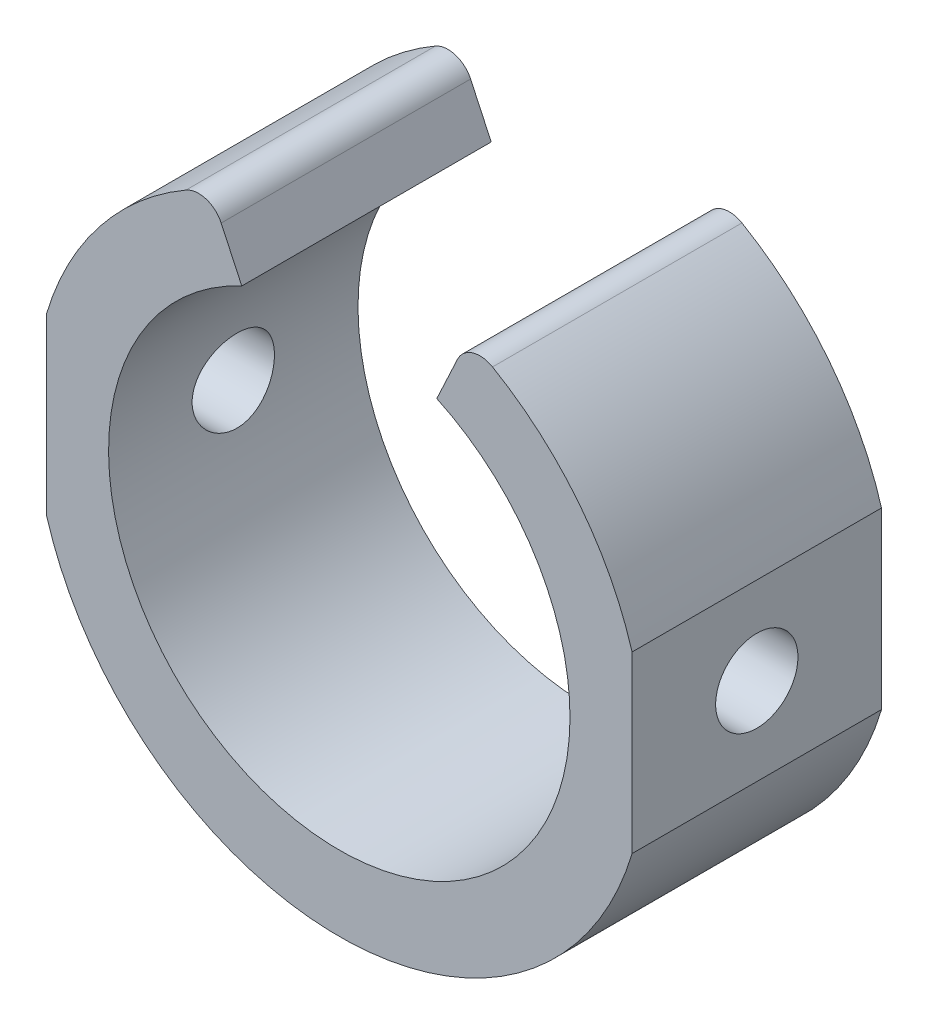
SolidWorks part; units mm, degrees
ref_plane "正面(Front)" through (0, 0, 0) normal (0, 0, 1) x (1, 0, 0)
ref_plane "平面(Top)" through (0, 0, 0) normal (0, 1, 0) x (1, 0, 0)
ref_plane "右側面(Right)" through (0, 0, 0) normal (1, 0, 0) x (0, 0, -1)
sketch "ｽｹｯﾁ1" plane through (0, 0, 0) normal (0, 0, 1) x (1, 0, 0)
  circle A0 centre (0, 0) radius 9.25
  circle A1 centre (0, 0) radius 12.25
  dimension "D1" = 18.5
  dimension "D2" = 3
extrude "ﾎﾞｽ - 押し出し1" add sketch "ｽｹｯﾁ1" along normal blind 10
sketch "ｽｹｯﾁ2" plane through (0, 0, 10) normal (0, 0, 1) x (1, 0, 0)
  line L0 (0, 0) -> (-7.0617, 15.144)
  line L1 (0, 0) -> (6.9061, 14.8103)
  line L2 (0, 0) -> (0, 17.4503) construction
  dimension "D1" = 25
extrude "ｶｯﾄ - 押し出し1" cut sketch "ｽｹｯﾁ2" against normal through all and the other way through all
sketch "ｽｹｯﾁ3" plane through (0, 0, 10) normal (0, 0, 1) x (1, 0, 0)
  line L0 (0, 0) -> (0, 8.3164) construction
  line L5 (-11.7394, -3.5) -> (-21.3781, -3.5)
  line L6 (-11.7394, -3.5) -> (-11.7394, 3.5)
  line L7 (-11.7394, 3.5) -> (-21.3781, 3.5)
  line L8 (-21.3781, -3.5) -> (-21.3781, 3.5)
  line L9 (11.7394, 3.5) -> (21.3781, 3.5)
  line L10 (21.3781, -3.5) -> (21.3781, 3.5)
  line L11 (11.7394, -3.5) -> (21.3781, -3.5)
  line L12 (11.7394, -3.5) -> (11.7394, 3.5)
  circle A1 centre (0, 0) radius 12.25 construction
  dimension "D1" = 7
extrude "ｶｯﾄ - 押し出し2" cut sketch "ｽｹｯﾁ3" against normal through all
sketch "ｽｹｯﾁ4" plane through (11.7394, 0, 0) normal (1, 0, 0) x (0, 0, -1)
  line L0 (0, 3.5) -> (-10, 3.5) construction
  circle A0 centre (-5, 0) radius 1.65
  point P5 (-5, 3.5)
  dimension "D1" = 3.3
extrude "ｶｯﾄ - 押し出し3" cut sketch "ｽｹｯﾁ4" against normal through all
fillet "ﾌｨﾚｯﾄ1" radius 1 2 edges at (5.1771, 11.1023, 5) (-5.1771, 11.1023, 5)
